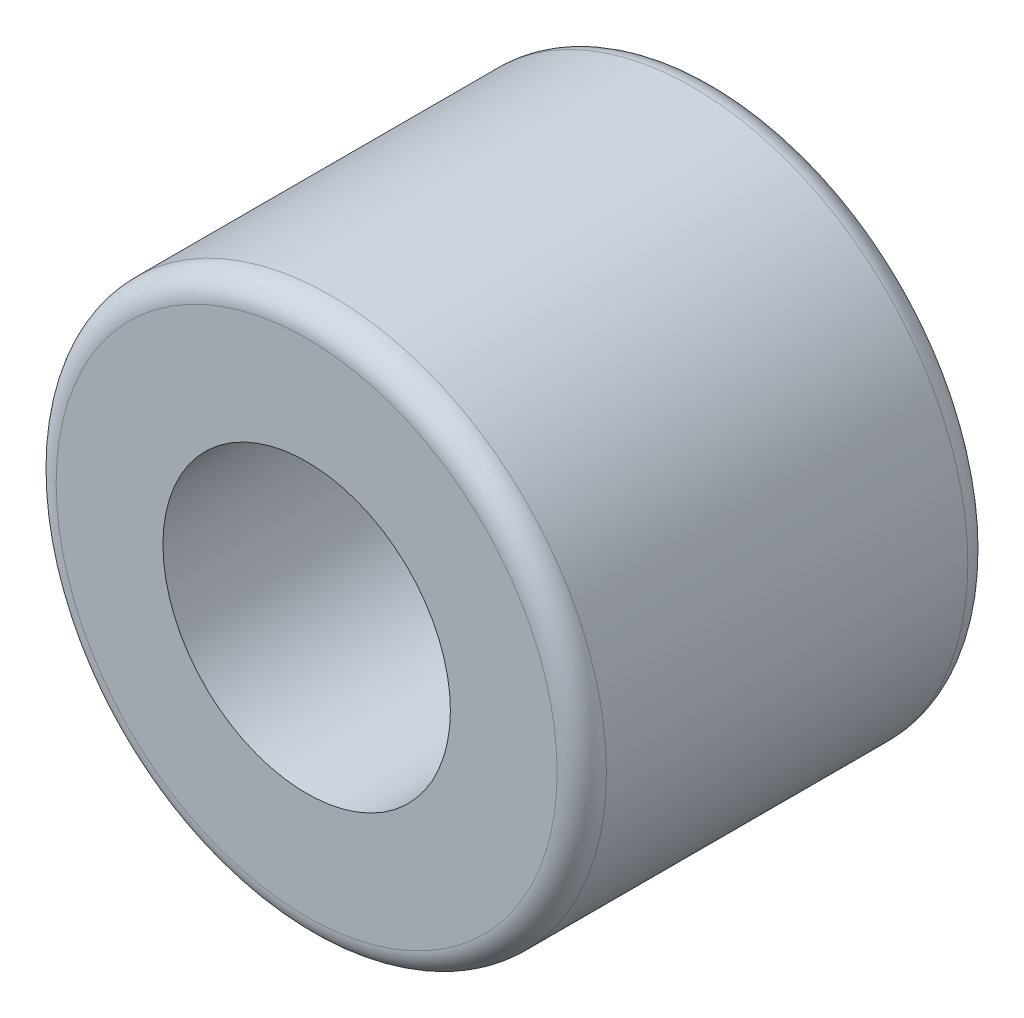
SolidWorks part; units mm, degrees
ref_plane "Ön Düzlem" through (0, 0, 0) normal (0, 0, 1) x (1, 0, 0)
ref_plane "Üst Düzlem" through (0, 0, 0) normal (0, 1, 0) x (1, 0, 0)
ref_plane "Sağ Düzlem" through (0, 0, 0) normal (1, 0, 0) x (0, 0, -1)
sketch "Çizim1" plane through (0, 0, 0) normal (0, 0, 1) x (1, 0, 0)
  circle A0 centre (0, 0) radius 8.509
  circle A1 centre (0, 0) radius 4.445
  dimension "D1" = 8.89
  dimension "D2" = 17.018
extrude "Yükseklik-Ekstrüzyon1" add sketch "Çizim1" along normal blind 12.7
fillet "Radyus1" radius 0.762 2 edges at (8.509, 0, 0) (8.509, 0, 12.7)
